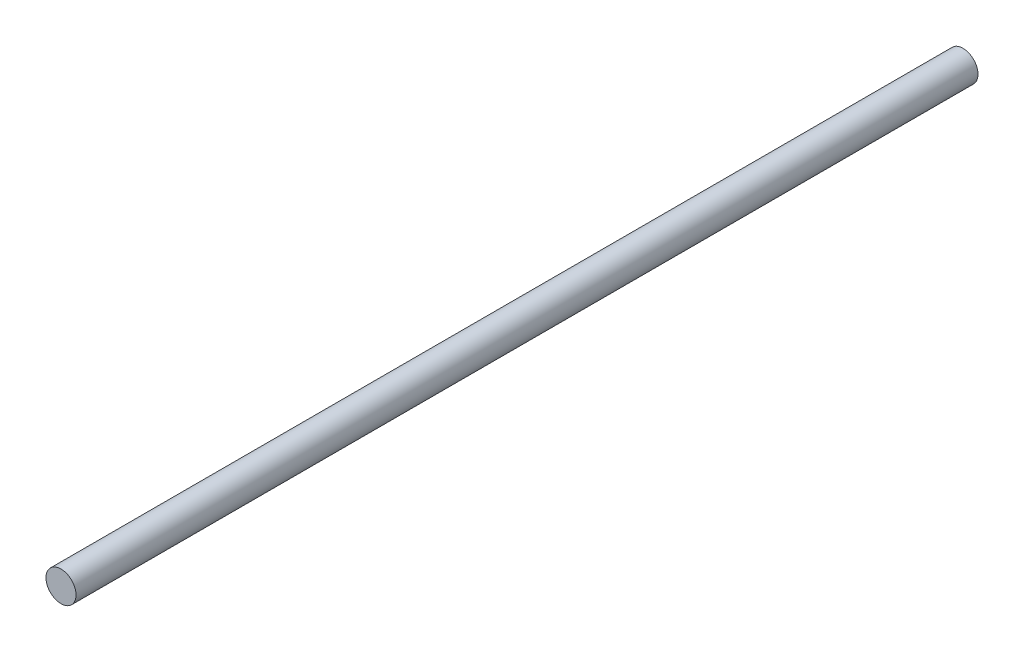
SolidWorks part; units mm, degrees
ref_plane "Alzado" through (0, 0, 0) normal (0, 0, 1) x (1, 0, 0)
ref_plane "Planta" through (0, 0, 0) normal (0, 1, 0) x (1, 0, 0)
ref_plane "Vista lateral" through (0, 0, 0) normal (1, 0, 0) x (0, 0, -1)
sketch "Sketch1" plane through (0, 0, 0) normal (0, 0, 1) x (1, 0, 0)
  circle A0 centre (0, 0) radius 1.5
  dimension "D1" = 3
extrude "Boss-Extrude1" add sketch "Sketch1" along normal blind 90
